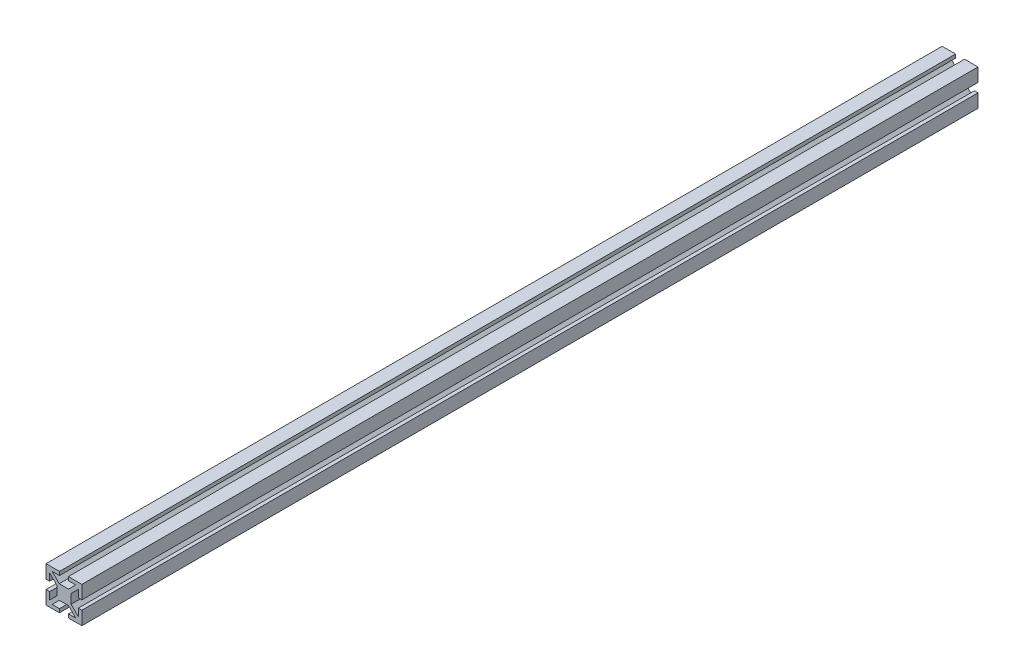
SolidWorks part; units mm, degrees
ref_plane "Front Plane" through (0, 0, 0) normal (0, 0, 1) x (1, 0, 0)
ref_plane "Top Plane" through (0, 0, 0) normal (0, 1, 0) x (1, 0, 0)
ref_plane "Right Plane" through (0, 0, 0) normal (1, 0, 0) x (0, 0, -1)
sketch "Sketch1" plane through (0, 0, 0) normal (0, 0, 1) x (1, 0, 0)
  line L0 (0, 4) -> (0, -4) construction
  line L1 (-2.5858, 4) -> (2.5858, 4)
  line L2 (-4, 2.5858) -> (-4, -2.5858)
  line L5 (-10, 10) -> (0, 0) construction
  line L6 (0, 10) -> (0, 4) construction
  line L7 (-4, 2.5858) -> (-8, 6.5858)
  line L8 (-6.5858, 8) -> (-2.5, 8)
  line L9 (-2.5, 8) -> (-2.5, 10)
  line L10 (-2.5, 10) -> (-10, 10)
  line L11 (-10, 10) -> (-10, 2.5)
  line L12 (-10, 2.5) -> (-8, 2.5)
  line L13 (-8, 2.5) -> (-8, 6.5858)
  line L14 (-4, 0) -> (4, 0) construction
  line L15 (-4, 0) -> (-10, 0) construction
  line L16 (-2.5858, 4) -> (-6.5858, 8)
  line L17 (-10, -10) -> (0, 0) construction
  line L18 (-2.5858, -4) -> (-6.5858, -8)
  line L19 (-8, -2.5) -> (-8, -6.5858)
  line L20 (-10, -2.5) -> (-8, -2.5)
  line L21 (-10, -10) -> (-10, -2.5)
  line L22 (-2.5, -10) -> (-10, -10)
  line L23 (-2.5, -8) -> (-2.5, -10)
  line L24 (-6.5858, -8) -> (-2.5, -8)
  line L25 (-4, -2.5858) -> (-8, -6.5858)
  line L26 (-2.5858, -4) -> (2.5858, -4)
  line L27 (10, -10) -> (0, 0) construction
  line L28 (4, 0) -> (10, 0) construction
  line L29 (10, 10) -> (0, 0) construction
  line L30 (4, -2.5858) -> (8, -6.5858)
  line L31 (6.5858, -8) -> (2.5, -8)
  line L32 (2.5, -8) -> (2.5, -10)
  line L33 (2.5, -10) -> (10, -10)
  line L34 (10, -10) -> (10, -2.5)
  line L35 (10, -2.5) -> (8, -2.5)
  line L36 (8, -2.5) -> (8, -6.5858)
  line L37 (2.5858, -4) -> (6.5858, -8)
  line L38 (2.5858, 4) -> (6.5858, 8)
  line L39 (8, 2.5) -> (8, 6.5858)
  line L40 (10, 2.5) -> (8, 2.5)
  line L41 (10, 10) -> (10, 2.5)
  line L42 (2.5, 10) -> (10, 10)
  line L43 (2.5, 8) -> (2.5, 10)
  line L44 (6.5858, 8) -> (2.5, 8)
  line L45 (4, 2.5858) -> (8, 6.5858)
  line L46 (4, 2.5858) -> (4, -2.5858)
  point P0 (0, 0)
  dimension "D1" = 10
  dimension "D2" = 4
  dimension "D3" = 2
  dimension "D4" = 10
  dimension "D5" = 2
  dimension "D6" = 2.5
  dimension "D7" = 2.5
  dimension "D8" = 4
  dimension "D9" = 1
  dimension "D10" = 1
extrude "Boss-Extrude1" add sketch "Sketch1" along normal mid plane 500
